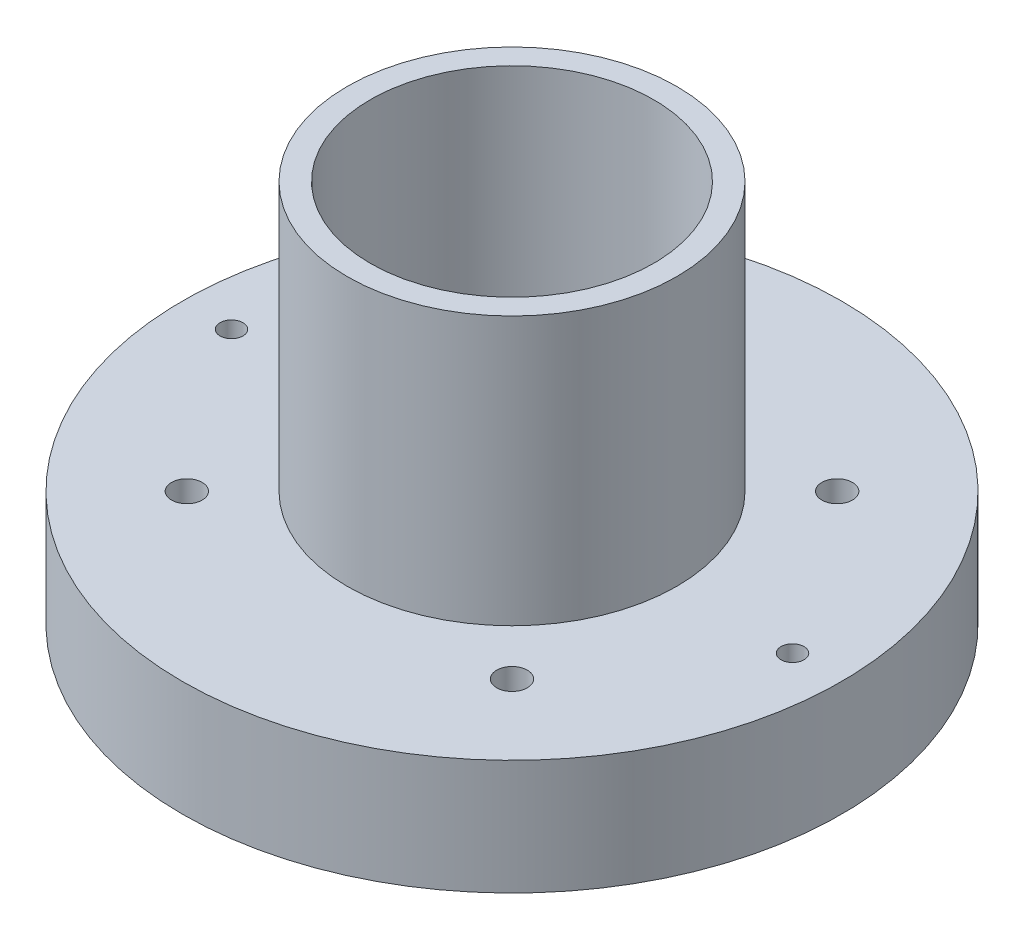
SolidWorks part; units mm, degrees
ref_plane "Front Plane" through (0, 0, 0) normal (0, 0, 1) x (1, 0, 0)
ref_plane "Top Plane" through (0, 0, 0) normal (0, 1, 0) x (1, 0, 0)
ref_plane "Right Plane" through (0, 0, 0) normal (1, 0, 0) x (0, 0, -1)
sketch "Sketch1" plane through (0, 0, 0) normal (0, 1, 0) x (1, 0, 0)
  circle A0 centre (0, 0) radius 43
  dimension "D1" = 86
extrude "Boss-Extrude1" add sketch "Sketch1" along normal blind 30
sketch "Sketch6" plane through (0, 0, 0) normal (0, -1, 0) x (1, 0, 0)
  circle A0 centre (0, 0) radius 25
  circle A1 centre (0, 0) radius 31.35
  dimension "D1" = 6.35
  dimension "D2" = 50
extrude "Cut-Extrude4" cut sketch "Sketch6" against normal blind 20
sketch "Sketch10" plane through (0, 30, 0) normal (0, 1, 0) x (1, 0, 0)
  line L0 (56.8446, 0) -> (-56.8446, 0) construction
  line L1 (0, 74.2115) -> (0, -74.2115) construction
  circle A0 centre (0, 0) radius 18.5
  circle A1 centre (0, 0) radius 21.5
  point P4 (0, 0)
  point P8 (0, 0)
  dimension "D1" = 37
  dimension "D2" = 0
  dimension "D3" = 3
extrude "Boss-Extrude2" add sketch "Sketch10" along normal blind 35
sketch "Sketch12" plane through (0, 30, 0) normal (0, 1, 0) x (1, 0, 0)
  line L0 (65.194, 0) -> (-65.194, 0) construction
  line L1 (0, -63.4304) -> (0, 63.4304) construction
  line L2 (-9.5, 0) -> (9.5, 0) construction
  line L3 (-9.5, 6) -> (9.5, 6)
  line L4 (-9.5, -6) -> (9.5, -6)
  arc A4 (-9.5, 6) -> (-9.5, -6) centre (-9.5, 0) ccw
  arc A5 (9.5, -6) -> (9.5, 6) centre (9.5, 0) ccw
  point P8 (0, 0)
  point P9 (0, 0)
  point P13 (0, 0)
  dimension "D1" = 0
  dimension "D2" = 9.5
  dimension "D3" = 12
extrude "Cut-Extrude6" cut sketch "Sketch12" against normal through all
hole_wizard "Ø3.0mm Dowel Hole1" positions "Sketch17" profile "Sketch18" hole size "Ø3.0" standard "ISO" end condition through all
sketch "Sketch17" plane through (0, 30, 0) normal (0, 1, 0) x (1, 0, 0)
  point P0 (-36.6, 0)
  point P2 (36.6, 0)
  dimension "D1" = 36.6
  dimension "D2" = 36.6
sketch "Sketch18" plane through (-36.6, 30, 0) normal (1, 0, 0) x (0, 0, 1)
  line L0 (0, 0) -> (0, 30)
  line L1 (0, 30) -> (1.5, 30)
  line L2 (1.5, 30) -> (1.5, 0)
  line L5 (1.5, 0) -> (0, 0)
  line L11 (0, -6.35) -> (0, 107.95) construction
  dimension "Thru Hole Dia." = 3
  dimension "Thru Hole Depth" = 30
hole_wizard "Ø4.0mm Dowel Hole2" positions "Sketch25" profile "Sketch26" hole size "Ø4.0" standard "ISO" end condition through all
sketch "Sketch25" plane through (0, 0, 0) normal (0, -1, 0) x (-1, 0, 0)
  line L1 (-77.8777, 0) -> (77.8777, 0) construction
  line L5 (0, 67.4991) -> (0, -67.4991) construction
  line L7 (-21.2132, -21.2132) -> (0, 0) construction
  point P0 (-21.2132, -21.2132)
  point P46 (21.2132, -21.2132)
  point P47 (-21.2132, 21.2132)
  point P48 (21.2132, 21.2132)
  dimension "D1" = 45
  dimension "D2" = 30
sketch "Sketch26" plane through (21.2132, 0, 21.2132) normal (1, 0, 0) x (0, 0, -1)
  line L0 (0, 0) -> (0, 65)
  line L1 (0, 65) -> (2, 65)
  line L2 (2, 65) -> (2, 0)
  line L5 (2, 0) -> (0, 0)
  line L11 (0, -6.35) -> (0, 107.95) construction
  dimension "Thru Hole Dia." = 4
  dimension "Thru Hole Depth" = 65
sketch "Sketch27" plane through (0, 0, 0) normal (0, -1, 0) x (1, 0, 0)
  circle A0 centre (0, 0) radius 51.9936
  dimension "D1" = 103.9872
extrude "Cut-Extrude7" cut sketch "Sketch27" against normal blind 15
